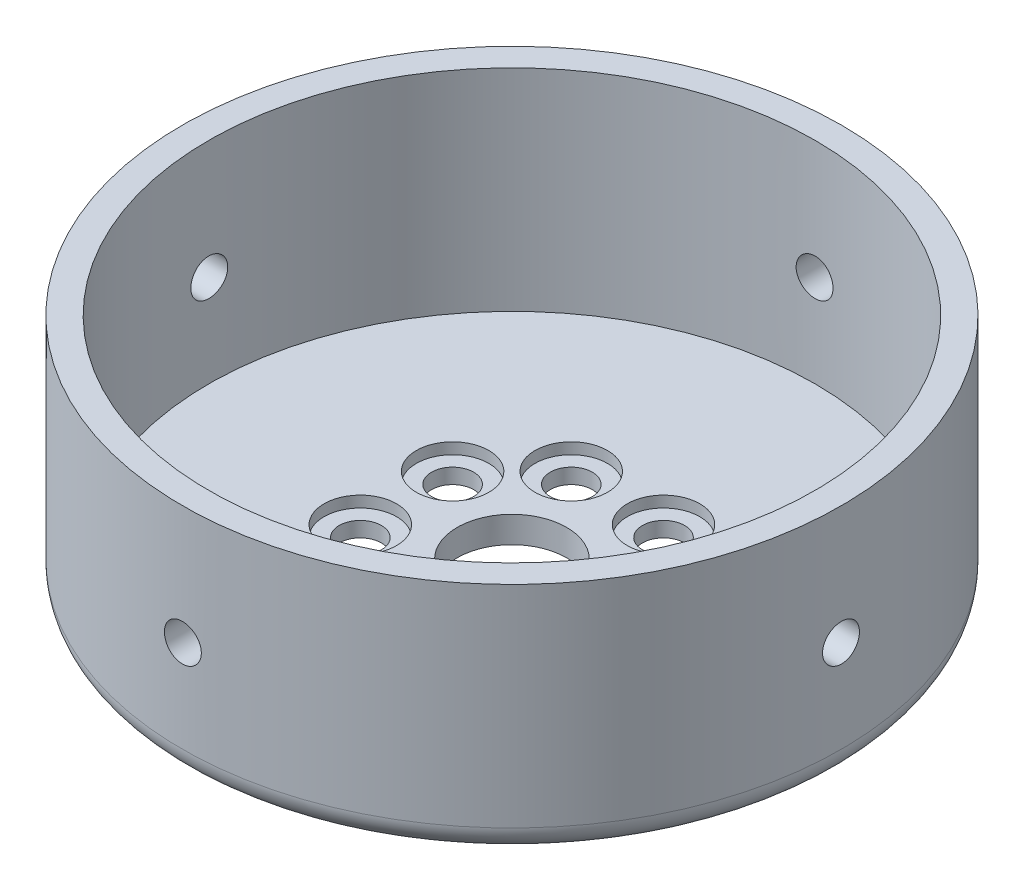
SolidWorks part; units mm, degrees
ref_plane "Front Plane" through (0, 0, 0) normal (0, 0, 1) x (1, 0, 0)
ref_plane "Top Plane" through (0, 0, 0) normal (0, 1, 0) x (1, 0, 0)
ref_plane "Right Plane" through (0, 0, 0) normal (1, 0, 0) x (0, 0, -1)
sketch "Sketch1" plane through (0, 0, 0) normal (0, 0, 1) x (1, 0, 0)
  line L0 (0, 0) -> (0, 2)
  line L1 (0, 2) -> (23, 2)
  line L2 (23, 2) -> (23, 18)
  line L3 (23, 18) -> (25, 18)
  line L4 (25, 18) -> (25, 0)
  line L5 (25, 0) -> (0, 0)
  dimension "D1" = 2
  dimension "D2" = 23
  dimension "D3" = 18
revolve "Revolve1" add sketch "Sketch1" angle 360 about L0
sketch "Sketch2" plane through (0, 2, 0) normal (0, 1, 0) x (1, 0, 0)
  circle A0 centre (0, 0) radius 4.15
  dimension "D1" = 8.3
extrude "Cut-Extrude1" cut sketch "Sketch2" against normal blind 10
sketch "Sketch3" plane through (0, 0, 0) normal (0, 0, 1) x (1, 0, 0)
  line L0 (0, 0) -> (0, 22.3249) construction
  line L1 (25, 9) -> (-25, 9) construction
  line L2 (25, 0) -> (25, 18) construction
  line L3 (-25, 18) -> (-25, 0) construction
  circle A0 centre (0, 9) radius 1.4
  dimension "D1" = 2.8
extrude "Cut-Extrude3" cut sketch "Sketch3" along normal mid plane 60
pattern_circular "CirPattern1" count 4 over 360 about axis through (0, 0, 0) along (0, -1, 0) of "Cut-Extrude3"
fillet "Fillet1" radius 2 1 edges at (0, 0, -25)
sketch "Sketch4" plane through (0, 0, 0) normal (0, -1, 0) x (1, 0, 0)
  line L0 (0, 0) -> (0, 26.8022) construction
  line L1 (0, 0) -> (36.748, 0) construction
  circle A0 centre (-3.5, 8) radius 1.6
  circle A1 centre (3.5, 8) radius 1.6
  circle A2 centre (-8, 3.5) radius 1.6
  circle A3 centre (8, 3.5) radius 1.6
  dimension "D2" = 3.2
  dimension "D1" = 7
  dimension "D3" = 16
  dimension "D4" = 8
  dimension "D5" = 3.5
extrude "Cut-Extrude4" cut sketch "Sketch4" against normal through all
sketch "Sketch6" plane through (0, 2, 0) normal (0, 1, 0) x (1, 0, 0)
  circle A0 centre (-8, -3.5) radius 2.75
  circle A1 centre (-3.5, -8) radius 2.75
  circle A2 centre (3.5, -8) radius 2.75
  circle A3 centre (8, -3.5) radius 2.75
  dimension "D1" = 5.5
extrude "Cut-Extrude5" cut sketch "Sketch6" against normal blind 0.85
mirror "Mirror1" about plane through (0, 0, 0) normal (0, 0, 1) of "Cut-Extrude4", "Cut-Extrude5"
